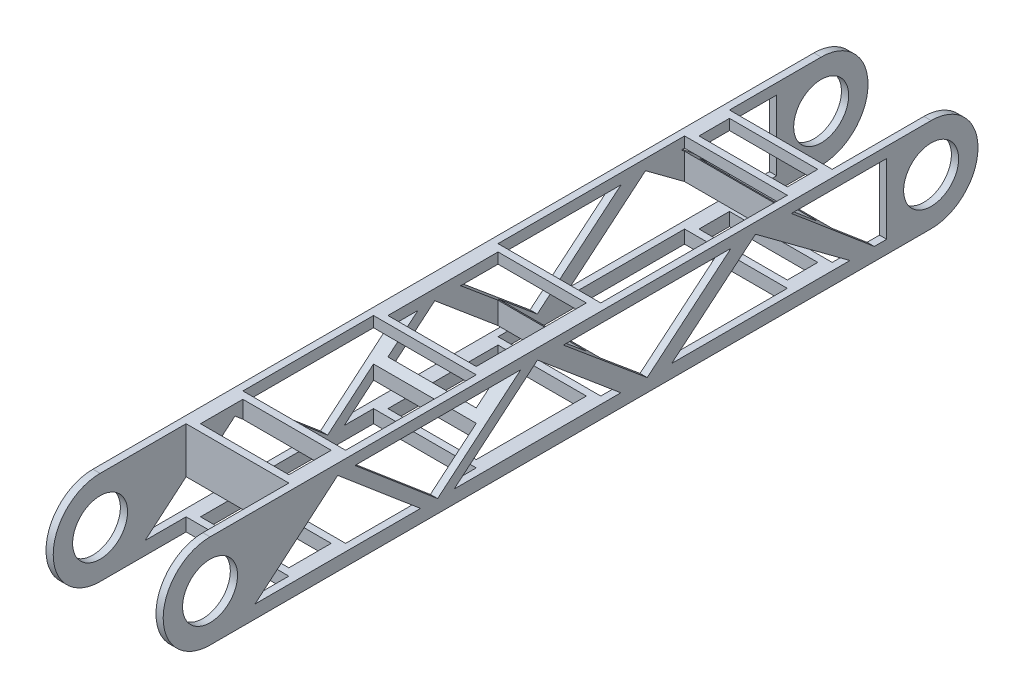
SolidWorks part; units mm, degrees
ref_plane "Alzado" through (0, 0, 0) normal (0, 0, 1) x (1, 0, 0)
ref_plane "Planta" through (0, 0, 0) normal (0, 1, 0) x (1, 0, 0)
ref_plane "Vista lateral" through (0, 0, 0) normal (1, 0, 0) x (0, 0, -1)
sketch "Croquis1" plane through (0, 0, 0) normal (1, 0, 0) x (0, 0, -1)
  line L1 (-200, 35) -> (200, 35)
  line L3 (-200, -35) -> (200, -35)
  arc A0 (-200, 35) -> (-200, -35) centre (-200, 0) ccw
  arc A1 (200, -35) -> (200, 35) centre (200, 0) ccw
  circle A2 centre (-200, 0) radius 15.25
  circle A3 centre (200, 0) radius 15.25
  point P0 (0, 0)
  dimension "D3" = 30.5
  dimension "D4" = 30.5
  dimension "D1" = 70
  dimension "D2" = 400
extrude "Saliente-Extruir1" add sketch "Croquis1" along normal blind 70
sketch "Croquis2" plane through (0, 35, 0) normal (0, 1, 0) x (1, 0, 0)
  line L0 (0, 200) -> (0, -200) construction
  line L1 (6.5, -236.7275) -> (63.5, -236.7275)
  line L2 (6.5, -236.7275) -> (6.5, -152.2903)
  line L3 (6.5, 238.6284) -> (63.5, 238.6284)
  line L4 (63.5, -236.7275) -> (63.5, -152.2903)
  line L5 (70, 200) -> (70, -200) construction
  line L6 (6.5, 149.1311) -> (63.5, 149.1311)
  line L7 (6.5, 124.2254) -> (63.5, 124.2254)
  line L8 (6.5, 20.7443) -> (63.5, 20.7443)
  line L9 (6.5, -152.2903) -> (63.5, -152.2903)
  line L10 (6.5, -120.8016) -> (63.5, -120.8016)
  line L11 (6.5, -48.318) -> (63.5, -48.318)
  line L12 (6.5, -120.8016) -> (6.5, -48.318)
  line L13 (63.5, -120.8016) -> (63.5, -48.318)
  line L14 (6.5, 20.7443) -> (6.5, 124.2254)
  line L15 (63.5, 20.7443) -> (63.5, 124.2254)
  line L16 (6.5, 149.1311) -> (6.5, 238.6284)
  line L17 (63.5, 149.1311) -> (63.5, 238.6284)
  dimension "D1" = 6.5
  dimension "D2" = 6.5
extrude "Cortar-Extruir1" cut sketch "Croquis2" against normal blind 70
sketch "Croquis3" plane through (70, 0, 0) normal (1, 0, 0) x (0, 0, -1)
  line L4 (200, 26) -> (-200, 26)
  line L5 (-200, -26) -> (200, -26)
  line L6 (200, 26) -> (-200, 26)
  line L7 (-200, -26) -> (200, -26)
  line L8 (200, 26) -> (-200, 26)
  line L9 (200, 26) -> (-200, 26)
  line L17 (-200, -35) -> (200, -35)
  line L18 (200, 35) -> (-200, 35)
  line L19 (-200, -35) -> (200, -35)
  line L20 (200, 35) -> (-200, 35)
  arc A4 (200, -26) -> (200, 26) centre (200, 0) ccw
  arc A5 (-200, 26) -> (-200, -26) centre (-200, 0) ccw
  arc A6 (200, -26) -> (200, 26) centre (200, 0) ccw
  arc A7 (-200, 26) -> (-200, -26) centre (-200, 0) ccw
  arc A12 (200, -35) -> (200, 35) centre (200, 0) ccw
  arc A13 (-200, 35) -> (-200, -35) centre (-200, 0) ccw
  arc A14 (200, -35) -> (200, 35) centre (200, 0) ccw
  arc A15 (-200, 35) -> (-200, -35) centre (-200, 0) ccw
  arc M11 (200, -35) -> (200, 35) centre (200, 0) ccw
  line M12 (200, 35) -> (-200, 35)
  arc M13 (-200, 35) -> (-200, -35) centre (-200, 0) ccw
  line M14 (-200, -35) -> (200, -35)
  dimension "D1" = 9
  dimension "D2" = 9
  dimension "D3" = 0
extrude "Cortar-Extruir2" cut sketch "Croquis3" against normal blind 70 contours A7 L6 A6 L7 M14 M11 M12 M13
sketch "Croquis4" plane through (70, 0, 0) normal (1, 0, 0) x (0, 0, -1)
  line L0 (-200, 26) -> (200, 26)
  line L1 (-200, -26) -> (200, -26)
  arc A0 (-200, 26) -> (-200, -26) centre (-200, 0) ccw
  circle A1 centre (-200, 0) radius 15.25
  arc A2 (200, -26) -> (200, 26) centre (200, 0) ccw
extrude "Cortar-Extruir3" cut sketch "Croquis4" against normal blind 2.5
sketch "Croquis5" plane through (0, 0, 0) normal (-1, 0, 0) x (0, 0, 1)
  line L0 (-200, 26) -> (200, 26)
  line L1 (-200, -26) -> (200, -26)
  arc A0 (200, -26) -> (200, 26) centre (200, 0) ccw
  circle A1 centre (200, 0) radius 15.25
  arc A2 (-200, 26) -> (-200, -26) centre (-200, 0) ccw
  circle A3 centre (-200, 0) radius 15.25
extrude "Cortar-Extruir4" cut sketch "Croquis5" against normal blind 2.5
sketch "Croquis6" plane through (0, 26, 0) normal (0, 1, 0) x (1, 0, 0)
  line L0 (10.5, -44.318) -> (59.5, -44.318)
  line L2 (10.5, 16.7443) -> (10.5, -44.318)
  line L4 (10.5, 16.7443) -> (59.5, 16.7443)
  line L5 (59.5, -44.318) -> (59.5, 16.7443)
extrude "Cortar-Extruir5" cut sketch "Croquis6" against normal blind 70
sketch "Croquis7" plane through (0, 26, 0) normal (0, 1, 0) x (1, 0, 0)
  line L0 (59.5, -148.2903) -> (59.5, -124.8016)
  line L1 (59.5, -124.8016) -> (10.5, -124.8016)
  line L6 (59.5, -148.2903) -> (10.5, -148.2903)
  line L7 (10.5, -124.8016) -> (10.5, -148.2903)
extrude "Cortar-Extruir6" cut sketch "Croquis7" against normal blind 70
sketch "Croquis8" plane through (0, 26, 0) normal (0, 1, 0) x (1, 0, 0)
  line L0 (59.5, 128.2254) -> (59.5, 145.1311)
  line L1 (10.5, 145.1311) -> (10.5, 128.2254)
  line L2 (10.5, 145.1311) -> (59.5, 145.1311)
  line L6 (10.5, 128.2254) -> (59.5, 128.2254)
extrude "Cortar-Extruir7" cut sketch "Croquis8" against normal blind 70
sketch "Croquis9" plane through (0, 0, 0) normal (1, 0, 0) x (0, 0, -1)
  line L0 (-175.0162, -18.7191) -> (-129.1758, 20.1193)
  line L1 (-64.5759, -18.7191) -> (27.8538, -18.7191)
  line L2 (-3.9533, 20.1193) -> (88.9697, 20.1193)
  line L3 (-175.0162, -18.7191) -> (-83.2525, -18.7191)
  line L4 (175.3399, 20.1193) -> (175.3399, -18.7191)
  line L5 (-129.1758, 20.1193) -> (-83.2525, -18.7191)
  line L6 (-119.6597, 20.1193) -> (-73.7719, -18.7191)
  line L7 (-73.7719, -18.7191) -> (-27.6622, 20.1193)
  line L8 (-64.5759, -18.7191) -> (-18.3611, 20.1193)
  line L9 (-18.3611, 20.1193) -> (27.8538, -18.7191)
  line L10 (-3.9533, 20.1193) -> (42.5082, -18.7191)
  line L11 (42.5082, -18.7191) -> (88.9697, 20.1193)
  line L12 (56.1007, -18.7191) -> (102.5622, 20.1193)
  line L13 (102.5622, 20.1193) -> (154.955, -18.7191)
  line L14 (168.4733, -18.7191) -> (122.5061, 20.1193)
  line L15 (56.1007, -18.7191) -> (154.955, -18.7191)
  line L16 (-119.6597, 20.1193) -> (-27.6622, 20.1193)
  line L17 (122.5061, 20.1193) -> (175.3399, 20.1193)
  line L18 (168.4733, -18.7191) -> (175.3399, -18.7191)
extrude "Cortar-Extruir8" cut sketch "Croquis9" along direction (1, 0, 0) on the side against the normal mid plane 150
